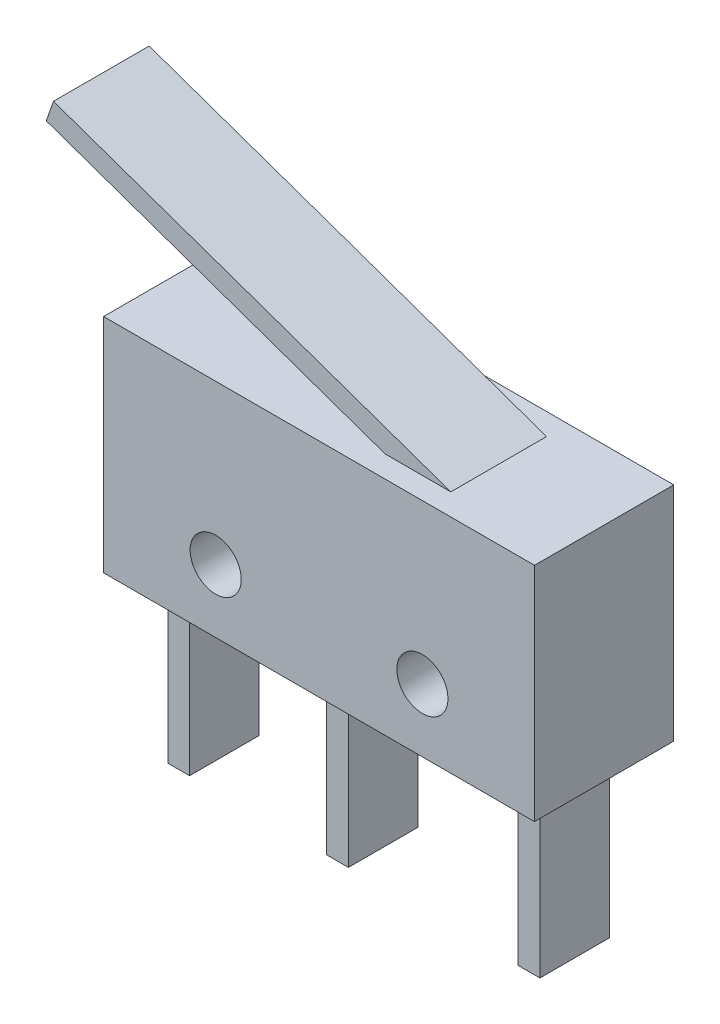
SolidWorks part; units mm, degrees
ref_plane "前视基准面" through (0, 0, 0) normal (0, 0, 1) x (1, 0, 0)
ref_plane "上视基准面" through (0, 0, 0) normal (0, 1, 0) x (1, 0, 0)
ref_plane "右视基准面" through (0, 0, 0) normal (1, 0, 0) x (0, 0, -1)
sketch "草图1" plane through (0, 0, 0) normal (0, 0, 1) x (1, 0, 0)
  line L1 (-9.9, -5.1) -> (9.9, -5.1)
  line L2 (-9.9, -5.1) -> (-9.9, 5.1)
  line L3 (-9.9, 5.1) -> (9.9, 5.1)
  line L4 (9.9, -5.1) -> (9.9, 5.1)
  line L5 (-9.9, -5.1) -> (9.9, 5.1) construction
  line L6 (-9.9, 5.1) -> (9.9, -5.1) construction
  point P0 (0, 0)
  dimension "D1" = 19.8
  dimension "D2" = 10.2
extrude "凸台-拉伸1" add sketch "草图1" along normal blind 6.4
sketch "草图2" plane through (0, 0, 0) normal (0, 0, -1) x (-1, 0, 0)
  line L0 (9.9, -5.1) -> (-9.9, -5.1) construction
  line L1 (0, 0) -> (0, -7.2834) construction
  circle A0 centre (-4.75, -2.2) radius 1.175
  circle A1 centre (4.75, -2.2) radius 1.175
  dimension "D1" = 2.35
  dimension "D2" = 2.9
  dimension "D3" = 9.5
extrude "切除-拉伸1" cut sketch "草图2" against normal through all
sketch "草图3" plane through (0, -5.1, 0) normal (0, -1, 0) x (-1, 0, 0)
  line L0 (-8.05, -1.6) -> (-8.05, -4.8)
  line L1 (0.75, -1.6) -> (0.75, -4.8)
  line L2 (8.05, -1.6) -> (8.05, -4.8)
  line L3 (-9.9, -6.4) -> (-9.9, 0) construction
  line L5 (9.9, 0) -> (-9.9, 0) construction
  line L6 (9.9, -6.4) -> (-9.9, -6.4) construction
  dimension "D1" = 8.8
  dimension "D2" = 7.3
  dimension "D3" = 1.85
  dimension "D4" = 1.6
  dimension "D5" = 1.6
extrude "拉伸-薄壁1" add sketch "草图3" along normal blind 7.7 thin thin type mid plane wall 1
sketch "草图4" plane through (0, 0, 0) normal (0, 0, -1) x (-1, 0, 0)
  line L0 (-5.0549, 5.1) -> (13.2034, 11.515)
  line L1 (-9.9, 5.1) -> (9.9, 5.1) construction
extrude "拉伸-薄壁2" add sketch "草图4" against normal blind 4.4 from offset 1 thin offset against normal yes
